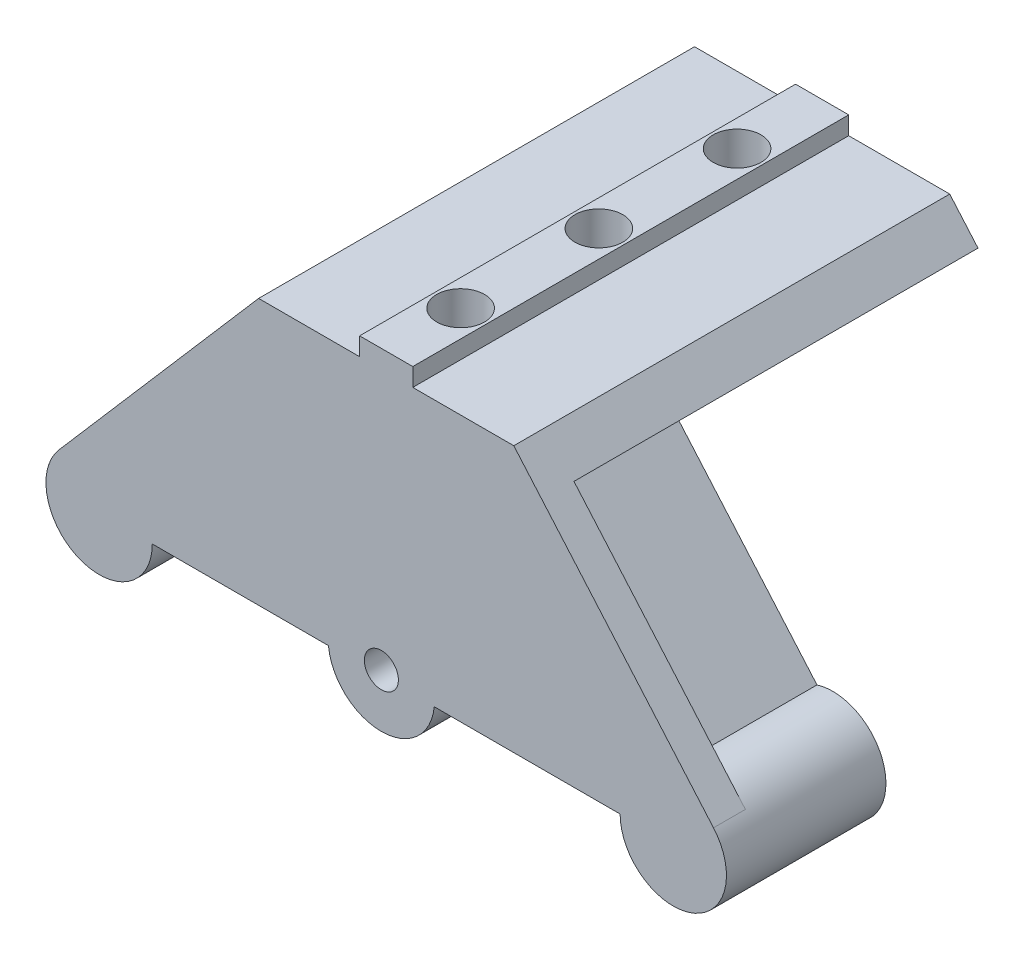
SolidWorks part; units mm, degrees
material "ABS"
ref_plane "Front Plane" through (0, 0, 0) normal (0, 0, 1) x (1, 0, 0)
ref_plane "Top Plane" through (0, 0, 0) normal (0, 1, 0) x (1, 0, 0)
ref_plane "Right Plane" through (0, 0, 0) normal (1, 0, 0) x (0, 0, -1)
sketch "Sketch1" plane through (0, 0, 0) normal (0, 0, 1) x (1, 0, 0)
  line L0 (-22, 0) -> (22, 0)
  line L1 (30.7828, 3.2697) -> (12, 25)
  line L2 (-12, 25) -> (-30.7828, 3.2697)
  line L3 (0, 0) -> (0, 25) construction
  line L4 (-12, 25) -> (12, 25)
  arc A0 (-30.7828, 3.2697) -> (-22, 0) centre (-27, 0) ccw
  arc A1 (22, 0) -> (30.7828, 3.2697) centre (27, 0) ccw
  dimension "D1" = 10
  dimension "D2" = 25
  dimension "D3" = 24
  dimension "D5" = 54
extrude "Boss-Extrude1" add sketch "Sketch1" against normal blind 3
sketch "Sketch2" plane through (0, 0, -3) normal (0, 0, -1) x (-1, 0, 0)
  line L0 (10.1198, 18) -> (-10.1198, 18)
  line L1 (12, 25) -> (30.7828, 3.2697) construction
  line L2 (12, 25) -> (-12, 25)
  line L3 (25.5164, 4.7748) -> (12.3895, 19.9618)
  line L4 (12.3895, 19.9618) -> (14.6591, 21.9236)
  line L5 (23.0398, 3.0524) -> (10.1198, 18)
  line L6 (0, 25) -> (0, 0) construction
  line L7 (-12.3895, 19.9618) -> (-14.6591, 21.9236)
  line L8 (-25.5164, 4.7748) -> (-12.3895, 19.9618)
  line L9 (-23.0398, 3.0524) -> (-10.1198, 18)
  line L12 (-30.7828, 3.2697) -> (-12, 25) construction
  line L13 (12, 25) -> (14.6591, 21.9236)
  line L16 (-14.6591, 21.9236) -> (-12, 25)
  arc A0 (23.0398, 3.0524) -> (25.5164, 4.7748) centre (27, 0) ccw
  arc A1 (-25.5164, 4.7748) -> (-23.0398, 3.0524) centre (-27, 0) ccw
  arc A4 (22, 0) -> (30.7828, 3.2697) centre (27, 0) ccw construction
  circle A5 centre (27, 0) radius 3.39
  circle A6 centre (-27, 0) radius 3.39
  dimension "D4" = 6.78
  dimension "D1" = 3
  dimension "D2" = 3
extrude "Boss-Extrude2" add sketch "Sketch2" along normal blind 12
sketch "Sketch3" plane through (0, 0, -15) normal (0, 0, -1) x (-1, 0, 0)
  line L0 (14.6591, 21.9236) -> (10.1198, 18)
  line L1 (14.6591, 21.9236) -> (12, 25) construction
  line L2 (10.1198, 18) -> (23.0398, 3.0524) construction
  line L3 (-10.1198, 18) -> (10.1198, 18) construction
  line L4 (10.1198, 18) -> (-10.1198, 18)
  line L5 (-10.1198, 18) -> (-14.6591, 21.9236)
  line L6 (-12, 25) -> (-14.6591, 21.9236) construction
  line L7 (-14.6591, 21.9236) -> (-12, 25)
  line L8 (14.6591, 21.9236) -> (12, 25)
  line L11 (12, 25) -> (-12, 25)
extrude "Boss-Extrude3" add sketch "Sketch3" along normal blind 26
sketch "Sketch7" plane through (0, 0, -41) normal (0, 0, -1) x (-1, 0, 0)
  line L0 (12, 25) -> (-12, 25) construction
  line L1 (-2.5, 25) -> (2.5, 25)
  line L2 (-2.5, 25) -> (-2.5, 26.7)
  line L3 (-2.5, 26.7) -> (2.5, 26.7)
  line L4 (2.5, 25) -> (2.5, 26.7)
  point P6 (0, 25)
  dimension "D1" = 5
  dimension "D2" = 1.7
extrude "Boss-Extrude5" add sketch "Sketch7" against normal up to vertex (41 mm away)
sketch "Sketch4" plane through (0, 25, 0) normal (0, 1, 0) x (-1, 0, 0)
  line L0 (0, -41) -> (0, 0) construction
  line L4 (-12, 0) -> (-2.5, 0) construction
  line L6 (-12, -41) -> (12, -41) construction
  line L7 (12, 0) -> (-12, 0) construction
  circle A0 centre (0, -33) radius 2.25
  circle A1 centre (0, -20) radius 2.25
  circle A2 centre (0, -7) radius 2.25
  dimension "D1" = 4.5
  dimension "D2" = 7
  dimension "D3" = 13
  dimension "D4" = 13
extrude "Cut-Extrude1" cut sketch "Sketch4" against normal mid plane 26
sketch "Sketch8" plane through (0, 18, 0) normal (0, -1, 0) x (-1, 0, 0)
  circle A0 centre (0, 33) radius 4
  dimension "D1" = 8
extrude "Cut-Extrude3" cut sketch "Sketch8" against normal blind 4.5
pattern_linear "LPattern1" count 3 spacing 13 along (0, 0, 1) of "Cut-Extrude3"
ref_plane "Plane1" through (0, 0, 0) normal (1, 0, 0) x (0, 0, -1)
sketch "Sketch5" plane through (0, 0, 0) normal (0, 0, 1) x (1, 0, 0)
  circle A0 centre (-0.4556, 0.4953) radius 5
  dimension "D2" = 10
  dimension "D1" = 0.4556
  dimension "D3" = 0.4953
extrude "Boss-Extrude4" add sketch "Sketch5" against normal blind 3
sketch "Sketch6" plane through (0, 0, 0) normal (0, 0, 1) x (1, 0, 0)
  circle A0 centre (-0.4556, 0.4953) radius 1.6
  arc A1 (-5.431, 0) -> (4.5198, 0) centre (-0.4556, 0.4953) ccw construction
  dimension "D1" = 3.2
extrude "Cut-Extrude2" cut sketch "Sketch6" against normal blind 3
